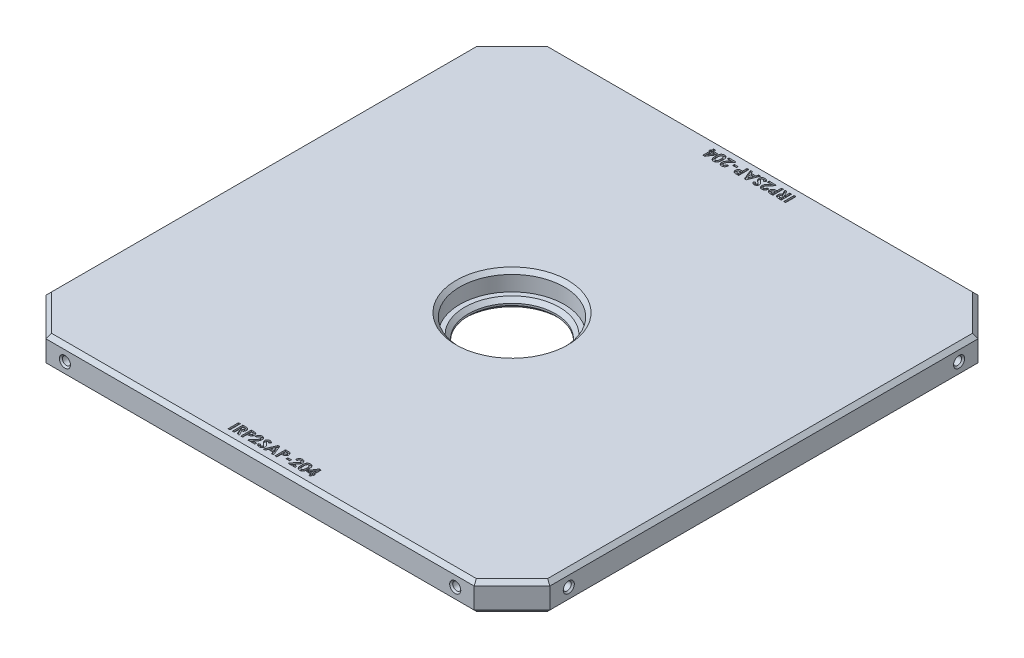
SolidWorks part; units mm, degrees
material "6061-T6 (SS)"
ref_plane "Front" through (0, 0, 0) normal (0, 0, 1) x (1, 0, 0)
ref_plane "Top" through (0, 0, 0) normal (0, 1, 0) x (1, 0, 0)
ref_plane "Right" through (0, 0, 0) normal (1, 0, 0) x (0, 0, -1)
sketch "Sketch1" plane through (0, 0, 0) normal (0, 1, 0) x (1, 0, 0)
  line L1 (-84.5344, -84.5344) -> (84.5344, -84.5344)
  line L2 (-84.5344, -84.5344) -> (-84.5344, 84.5344)
  line L3 (-84.5344, 84.5344) -> (84.5344, 84.5344)
  line L4 (84.5344, -84.5344) -> (84.5344, 84.5344)
  line L5 (-84.5344, -84.5344) -> (84.5344, 84.5344) construction
  line L6 (-84.5344, 84.5344) -> (84.5344, -84.5344) construction
  line L7 (23.5712, -23.5712) -> (-23.5712, -23.5712) construction
  line L8 (23.5712, -23.5712) -> (23.5712, 23.5712) construction
  line L9 (23.5712, 23.5712) -> (-23.5712, 23.5712) construction
  line L10 (-23.5712, -23.5712) -> (-23.5712, 23.5712) construction
  line L11 (23.5712, -23.5712) -> (-23.5712, 23.5712) construction
  line L12 (23.5712, 23.5712) -> (-23.5712, -23.5712) construction
  circle A0 centre (0, 0) radius 17.5
  circle A1 centre (-23.5712, 23.5712) radius 3.175 construction
  circle A2 centre (23.5712, 23.5712) radius 3.175 construction
  circle A3 centre (23.5712, -23.5712) radius 3.175 construction
  circle A4 centre (-23.5712, -23.5712) radius 3.175 construction
  point P0 (0, 0)
  dimension "D4" = 34.9999
  dimension "D5" = 6.35
  dimension "D1" = 169.0687
  dimension "D3" = 47.1424
extrude "Boss-Extrude1" add sketch "Sketch1" along normal blind 9.525
chamfer "Chamfer1" distance 12.7 angle 45 4 edges at (-84.5344, 4.7625, -84.5344) (84.5344, 4.7625, -84.5344) (84.5344, 4.7625, 84.5344) (-84.5344, 4.7625, 84.5344)
hole_wizard "#6-32 Tapped Hole2" positions "Sketch3" profile "Sketch4" tap size "#6-32" standard "ANSI Inch"
sketch "Sketch3" plane through (0, 0, 84.5344) normal (0, 0, 1) x (1, 0, 0)
  line L0 (-71.8344, 4.7625) -> (-65.4844, 4.7625) construction
  line L1 (-71.8344, 9.525) -> (-71.8344, 0) construction
  line L2 (-65.4844, 4.7625) -> (65.4844, 4.7625) construction
  line L3 (65.4844, 4.7625) -> (71.8344, 4.7625) construction
  line L4 (71.8344, 0) -> (71.8344, 9.525) construction
  point P0 (-65.4844, 4.7625)
  point P2 (65.4844, 4.7625)
  dimension "D1" = 130.9688
sketch "Sketch4" plane through (-65.4844, 4.7625, 84.5344) normal (1, 0, 0) x (0, -1, 0)
  line L0 (0, 0) -> (0, 16.6877)
  line L1 (0, 16.6877) -> (1.3525, 15.875)
  line L2 (1.3525, 15.875) -> (1.3525, 0)
  line L5 (1.3525, 0) -> (0, 0)
  line L10 (0, 16.6877) -> (-1.3526, 15.875) construction
  line L11 (0, -6.35) -> (0, 107.95) construction
  dimension "Tap Drill Dia." = 2.7051
  dimension "Tap Drill Depth" = 15.875
  dimension "Drill Angle" = 118
cosmetic thread "Hole Thread1" parameters "D1"=15.0825, "D2"=3.5052
cosmetic thread "Hole Thread2" parameters "D1"=15.0825, "D2"=3.5052
pattern_circular "CirPattern1" count 4 over 360 about axis through (0, 9.525, 0) along (0, 1, 0) of "#6-32 Tapped Hole2"
cosmetic thread "Hole Thread3" parameters "D1"=15.0825, "D2"=3.5052
cosmetic thread "Hole Thread4" parameters "D1"=15.0825, "D2"=3.5052
cosmetic thread "Hole Thread5" parameters "D1"=15.0825, "D2"=3.5052
cosmetic thread "Hole Thread6" parameters "D1"=15.0825, "D2"=3.5052
sketch "Sketch9" plane through (0, 0, 0) normal (0, -1, 0) x (1, 0, 0)
  circle A0 centre (0, 0) radius 14.605
  circle A1 centre (0, 0) radius 17.5
  circle A2 centre (0, 0) radius 17.5 construction
  dimension "D1" = 29.21
extrude "Boss-Extrude2" add sketch "Sketch9" against normal blind 3.175
chamfer "Chamfer2" distance 0.508 angle 45 8 edges at (-84.5344, 4.7625, 66.8369) (-84.5344, 4.7625, -64.1318) (-66.8369, 4.7625, -84.5344) (64.1318, 4.7625, -84.5344) (84.5344, 4.7625, -66.8369) (-64.1318, 4.7625, 84.5344) (84.5344, 4.7625, 64.1318) (66.8369, 4.7625, 84.5344)
chamfer "Chamfer3" distance 1.27 angle 45 19 edges at (-78.1844, 9.525, 78.1844) (-78.1844, 0, 78.1844) (0, 0, 84.5344) (0, 9.525, 84.5344) (78.1844, 9.525, 78.1844) (78.1844, 0, 78.1844) (84.5344, 0, 0) (84.5344, 9.525, 0) (78.1844, 9.525, -78.1844) (78.1844, 0, -78.1844) (0, 0, -84.5344) (0, 9.525, -84.5344) (-78.1844, 9.525, -78.1844) (-78.1844, 0, -78.1844) (-84.5344, 9.525, 0) (-84.5344, 0, 0) (0, 9.525, 17.5) (0, 3.175, -14.605) (0, 0, -14.605)
sketch "Sketch7" plane through (0, 0, 0) normal (0, -1, 0) x (1, 0, 0)
  line L0 (-83.2644, 81.3594) -> (83.2644, 81.3594) construction
  line L1 (-83.2644, 71.3083) -> (-83.2644, -71.3083) construction
  line L2 (83.2644, -71.3083) -> (83.2644, 71.3083) construction
  line L3 (-83.2644, -81.3594) -> (84.5344, -81.3594) construction
  line L4 (84.5344, 71.8344) -> (84.5344, -71.8344) construction
  line L5 (-71.8344, 84.5344) -> (71.8344, 84.5344) construction
  line L6 (71.8344, -84.5344) -> (-71.8344, -84.5344) construction
  text T0 "<b>IRP2SAP-204</b>"
  text T1 "<b>IRP2SAP-204</b>"
  dimension "D1" = 3.175
  dimension "D2" = 3.175
extrude "Cut-Extrude1" cut sketch "Sketch7" against normal blind 0.508
sketch "Sketch8" plane through (0, 9.525, 0) normal (0, 1, 0) x (1, 0, 0)
  line L0 (-84.5344, 81.3594) -> (84.5344, 81.3594) construction
  line L1 (-84.5344, -71.8344) -> (-84.5344, 71.8344) construction
  line L2 (84.5344, 71.8344) -> (84.5344, -71.8344) construction
  line L3 (-84.5344, -81.3594) -> (84.5344, -81.3594) construction
  line L4 (-71.8344, 84.5344) -> (71.8344, 84.5344) construction
  line L5 (71.8344, -84.5344) -> (-71.8344, -84.5344) construction
  text T0 "<b>IRP2SAP-204</b>"
  text T1 "<b>IRP2SAP-204</b>"
  dimension "D1" = 3.175
  dimension "D2" = 3.175
extrude "Cut-Extrude2" cut sketch "Sketch8" against normal blind 0.508
